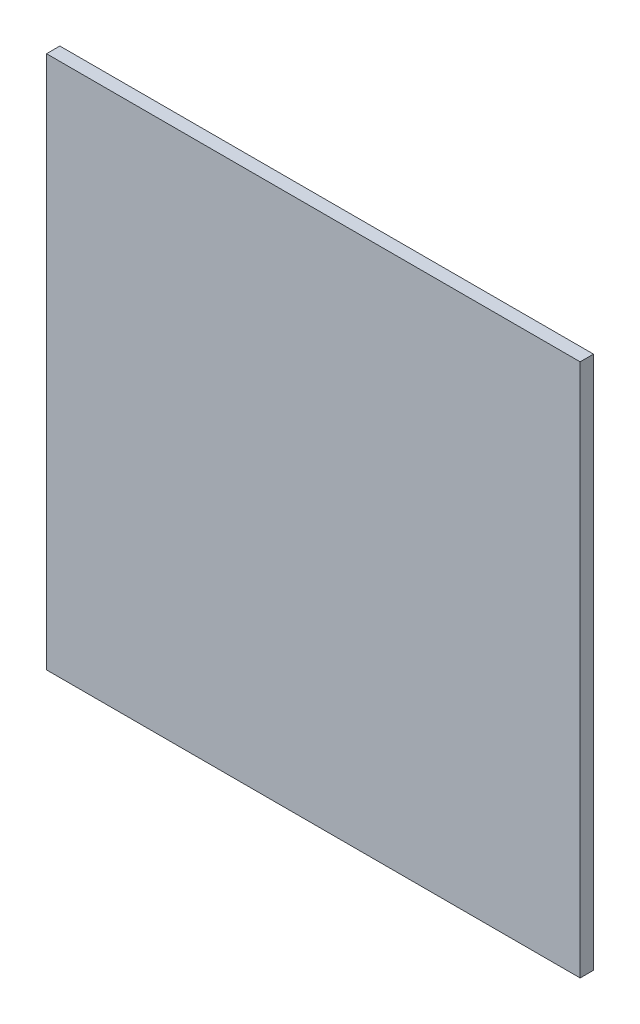
SolidWorks part; units mm, degrees
ref_plane "Front Plane" through (0, 0, 0) normal (0, 0, 1) x (1, 0, 0)
ref_plane "Top Plane" through (0, 0, 0) normal (0, 1, 0) x (1, 0, 0)
ref_plane "Right Plane" through (0, 0, 0) normal (1, 0, 0) x (0, 0, -1)
sketch "Sketch1" plane through (0, 0, 0) normal (0, 0, 1) x (1, 0, 0)
  line L1 (-0.2, -0.2) -> (0.2, -0.2)
  line L2 (-0.2, -0.2) -> (-0.2, 0.2)
  line L3 (-0.2, 0.2) -> (0.2, 0.2)
  line L4 (0.2, -0.2) -> (0.2, 0.2)
extrude "Boss-Extrude1" add sketch "Sketch1" along normal blind 0.01
